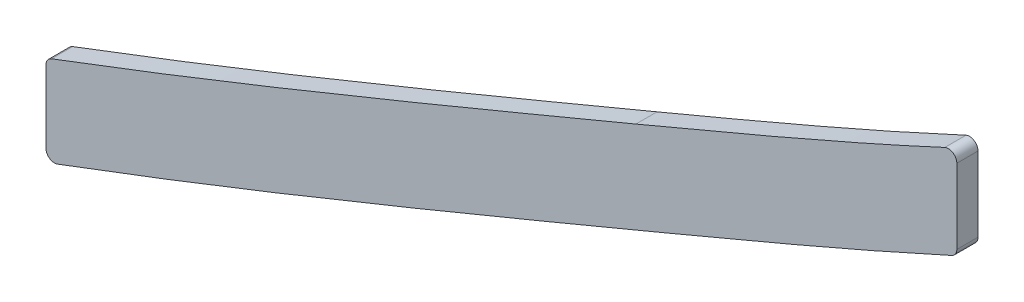
SolidWorks part; units mm, degrees
material "Balsa"
ref_plane "Front Plane" through (0, 0, 0) normal (0, 0, 1) x (1, 0, 0)
ref_plane "Top Plane" through (0, 0, 0) normal (0, 1, 0) x (1, 0, 0)
ref_plane "Right Plane" through (0, 0, 0) normal (1, 0, 0) x (0, 0, -1)
sketch "Sketch1" plane through (0, 0, 0) normal (0, 0, 1) x (1, 0, 0)
  line L0 (129.1265, 126.0779) -> (45.2335, 95.7177) construction
  line L1 (0, 0) -> (0, 656.1291) construction
  line L2 (1046.2855, -53.4707) -> (499.61, -53.4707)
  line L3 (210.5585, 160.3278) -> (162.5016, 140.2562) construction
  line L4 (103.1875, 116.7756) -> (103.1875, 13.8211)
  line L5 (239.7125, 173.3723) -> (239.7125, 18.8603)
  line L6 (239.2308, 173.1465) -> (239.7125, 173.3723)
  line L8 (244.6214, 161.6473) -> (245.1031, 161.8731) construction
  arc A3 (36.5452, 91.5722) -> (50.6762, 98.5918) centre (72.503, 36.9197) cw
  arc A4 (33.5941, 89.512) -> (36.5452, 91.5722) centre (72.5029, 36.9192) cw
  arc A5 (26.5879, 83.5209) -> (26.7433, 83.6735) centre (72.5028, 36.9189) cw
  spline S0 degree 3 poles (90.5238, 112.1079) (125.4792, 124.758) (161.5722, 139.868) (191.6078, 152.4128) knots 0 0 0 0 1 1 1 1
  spline S1 degree 1 poles (94.8455, 100.1658) (196.5024, 140.6938) knots 0 0 1 1 construction
  spline S2 degree 1 poles (196.5024, 140.6938) (244.6214, 161.6473) knots 0 0 1 1 construction
  spline S3 degree 3 poles (94.8455, 100.1658) (99.2852, 101.7725) (108.1262, 105.0368) (121.4387, 110.1165) (134.6545, 115.2971) (147.7092, 120.5264) (160.5147, 125.7437) (170.9096, 130.0328) (179.0169, 133.3991) (184.9834, 135.8842) (189.8481, 137.9146) (193.6777, 139.514) (195.5579, 140.2994) (196.5024, 140.6938) knots 0 0 0 0 0.125 0.25 0.375 0.5 0.625 0.75 0.8125 0.875 0.9375 0.96875 1 1 1 1
  spline S4 degree 3 poles (196.5024, 140.6938) (200.4723, 142.3519) (208.3835, 145.6702) (220.3642, 150.772) (230.4226, 155.1671) (238.5139, 158.8124) (242.5935, 160.6966) (244.6214, 161.6473) knots 14.81781 14.81781 14.81781 14.81781 16.034279 17.250748 18.467217 19.075451 19.683685 19.683685 19.683685 19.683685
  spline S8 degree 5 poles (191.6078, 152.4128) (201.0734, 156.3662) (210.5667, 160.3662) (220.0964, 164.4424) (229.6613, 168.6605) (239.2308, 173.1465) knots 14.81781 14.81781 14.81781 14.81781 14.81781 14.81781 19.683685 19.683685 19.683685 19.683685 19.683685 19.683685 weights 1 1 1 1 1 1
  spline S9 degree 5 poles (50.6762, 98.5918) (58.5981, 101.1149) (66.52, 103.702) (74.4715, 106.3907) (82.4705, 109.1935) (90.5238, 112.1079) knots 0 0 0 0 0 0 4.296847 4.296847 4.296847 4.296847 4.296847 4.296847 weights 1 1 1 1 1 1
  spline S10 degree 5 poles (26.7433, 83.6735) (28.0126, 84.9158) (29.3241, 86.115) (30.6979, 87.2902) (32.127, 88.4267) (33.5941, 89.512) knots 0 0 0 0 0 0 0.963167 0.963167 0.963167 0.963167 0.963167 0.963167 weights 1 1 1 1 1 1
  spline S11 degree 5 poles (18.4363, 73.7529) (19.8463, 75.8225) (21.3553, 77.8246) (22.9948, 79.8016) (24.7465, 81.7067) (26.5879, 83.5209) knots 0 0 0 0 0 0 1.402615 1.402615 1.402615 1.402615 1.402615 1.402615 weights 1 1 1 1 1 1
  spline S12 degree 5 poles (818.067, 264.7065) (827.0431, 263.4992) (836.0291, 262.3734) (845.0868, 261.3058) (891.3865, 256.087) (937.6862, 251.7792) (973.4521, 248.2277) (1071.9467, 239.0511) (1170.4413, 229.7315) (1231.7919, 224.5039) (1324.8993, 216.7906) (1418.0067, 209.0401) (1449.7429, 206.3618) (1636.9286, 190.5211) (1824.1143, 175.4092) (1979.9669, 164.2997) (2156.2686, 150.4144) (2332.5703, 133.8572) (2354.213, 131.7851) (2436.3555, 123.724) (2518.4981, 114.8591) (2579.4813, 107.7425) (2639.6368, 100.3834) (2699.7923, 92.6045) knots 77.930822 77.930822 77.930822 77.930822 77.930822 77.930822 82.465793 82.465793 82.465793 100.79329 100.79329 100.79329 131.098954 131.098954 131.098954 146.769198 146.769198 146.769198 223.533959 223.533959 223.533959 233.943117 233.943117 233.943117 264.216209 264.216209 264.216209 264.216209 264.216209 264.216209 weights 1 1 1 1 1 1 1 1 1 1 1 1 1 1 1 1 1 1 1 1 1 1 1 1
  spline S13 degree 5 poles (241.4251, -53.4707) (224.2869, -53.4707) (207.1495, -53.4673) (190.2039, -52.6866) (151.6561, -49.0319) (113.1083, -41.5037) (91.9499, -36.3426) (71.313, -30.9696) (50.6762, -24.7565) knots 0 0 0 0 0 0 8.713816 8.713816 8.713816 19.90683 19.90683 19.90683 19.90683 19.90683 19.90683 weights 1 1 1 1 1 1 1 1 1
  spline S14 degree 5 poles (499.61, -53.4707) (492.1368, -53.4707) (484.7543, -53.4707) (477.443, -53.4707) (448.5166, -53.4707) (419.5901, -53.4707) (398.3681, -53.4707) (355.6475, -53.4707) (312.927, -53.4707) (289.2351, -53.4703) (265.365, -53.4707) (241.4948, -53.4707) (241.4716, -53.4707) (241.4484, -53.4707) (241.4251, -53.4707) knots 19.90683 19.90683 19.90683 19.90683 19.90683 19.90683 23.637897 23.637897 23.637897 34.276546 34.276546 34.276546 46.401341 46.401341 46.401341 46.413154 46.413154 46.413154 46.413154 46.413154 46.413154 weights 1 1 1 1 1 1 1 1 1 1 1 1 1 1 1
  spline S15 degree 5 poles (2699.7923, -7.5245) (2639.6368, -11.6572) (2579.4813, -15.4358) (2518.4981, -19.1485) (2436.3555, -23.2524) (2354.213, -26.6315) (2332.5703, -27.481) (2156.2686, -34.3778) (1979.9669, -41.6286) (1824.1143, -52.7713) (1636.9286, -53.5796) (1449.7429, -53.454) (1418.0067, -53.4707) (1324.8993, -53.4707) (1231.7919, -53.4707) (1170.4413, -53.4707) (1108.7841, -53.4707) (1047.1269, -53.4707) (1046.8464, -53.4707) (1046.5659, -53.4707) (1046.2855, -53.4707) knots 100.654805 100.654805 100.654805 100.654805 100.654805 100.654805 130.927897 130.927897 130.927897 141.337055 141.337055 141.337055 218.101815 218.101815 218.101815 233.772059 233.772059 233.772059 264.077723 264.077723 264.077723 264.216209 264.216209 264.216209 264.216209 264.216209 264.216209 weights 1 1 1 1 1 1 1 1 1 1 1 1 1 1 1 1 1 1 1 1 1
  point P2 (0, 0)
  dimension "D1" = 72.503
  dimension "D2" = 1046.2855
  dimension "D3" = 818.067
  dimension "D4" = 103.1875
  dimension "D5" = 239.7125
  dimension "D6" = 12.7
extrude "Boss-Extrude1" add sketch "Sketch1" against normal mid plane 3.175 contours S8 S0 L4 S3 S4 L5 L6
fillet "Fillet1" radius 1.27 4 edges at (239.7125, 159.3721, 0) (239.7125, 173.3723, 0) (103.1875, 103.2218, 0) (103.1875, 116.7756, 0)
